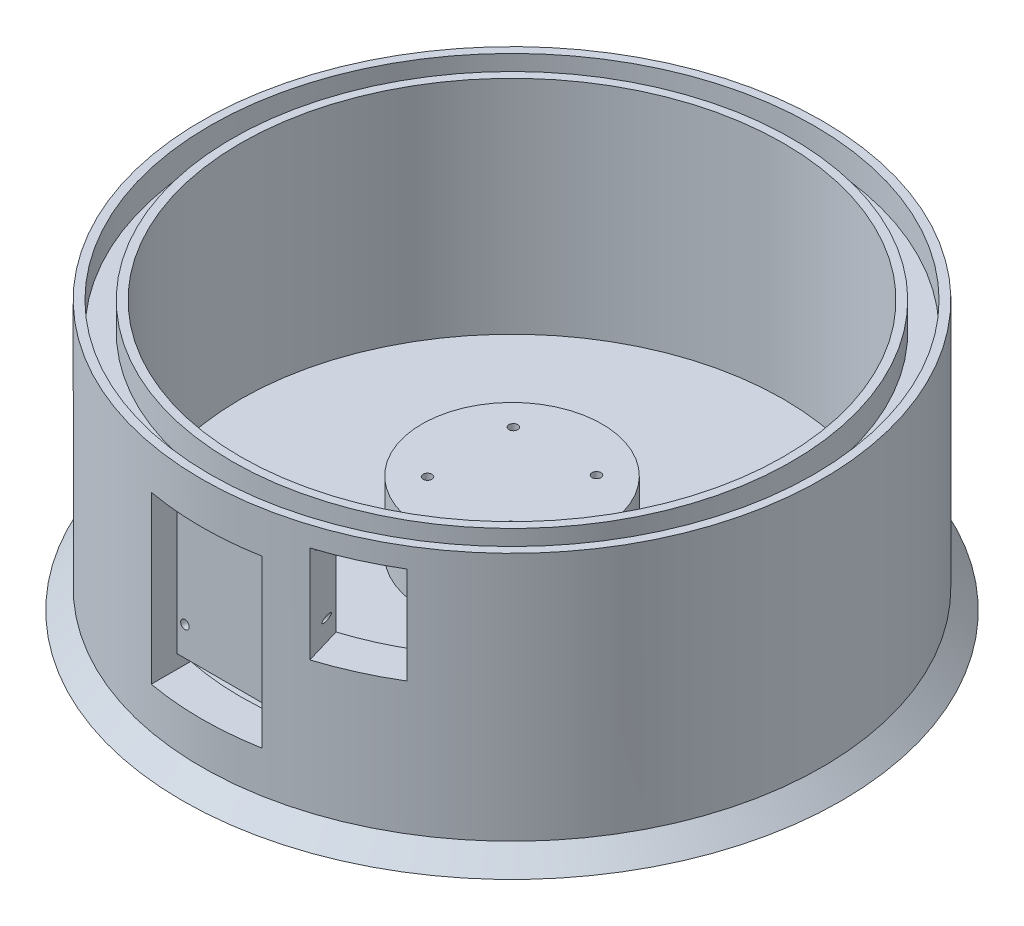
SolidWorks part; units mm, degrees
material "ABS"
ref_plane "Front Plane" through (0, 0, 0) normal (0, 0, 1) x (1, 0, 0)
ref_plane "Top Plane" through (0, 0, 0) normal (0, 1, 0) x (1, 0, 0)
ref_plane "Right Plane" through (0, 0, 0) normal (1, 0, 0) x (0, 0, -1)
sketch "Sketch1" plane through (0, 0, 0) normal (0, 1, 0) x (1, 0, 0)
  circle A1 centre (0, 0) radius 112
extrude "Boss-Extrude3" add sketch "Sketch1" along normal blind 90
ref_plane "Plane1" through (0, 0, 105) normal (0, 0, 1) x (1, 0, 0)
sketch "Sketch9" plane through (0, 90, 0) normal (0, 1, 0) x (1, 0, 0)
  circle A5 centre (0, 0) radius 101
  circle A7 centre (0, 0) radius 109
extrude "Cut-Extrude6" cut sketch "Sketch9" against normal blind 10
sketch "Sketch4" plane through (0, 0, 105) normal (0, 0, 1) x (1, 0, 0)
  line L26 (-20, 75) -> (20, 75)
  line L27 (-20, 75) -> (-20, 15)
  line L28 (-20, 15) -> (20, 15)
  line L29 (20, 75) -> (20, 15)
  line L30 (-20, 75) -> (20, 15) construction
  line L31 (-20, 15) -> (20, 75) construction
  point P5 (0, 45)
  dimension "D1" = 60
  dimension "D2" = 40
  dimension "D3" = 45
extrude "Cut-Extrude2" cut sketch "Sketch4" along normal blind 26 and the other way blind 4
sketch "Sketch12" plane through (0, 0, 0) normal (0, -1, 0) x (1, 0, 0)
  circle A1 centre (0, 0) radius 112
  circle A2 centre (0, 0) radius 112
  dimension "D1" = 0
extrude "Boss-Extrude4" add sketch "Sketch12" along normal blind 7 draft 45 draft outward yes
sketch "Sketch13" plane through (0, 90, 0) normal (0, 1, 0) x (1, 0, 0)
  circle A0 centre (0, 0) radius 98
extrude "Cut-Extrude8" cut sketch "Sketch13" against normal blind 80 contours A0
sketch "Sketch14" plane through (0, 0, 101) normal (0, 0, 1) x (1, 0, 0)
  circle A0 centre (-31.25, 55.25) radius 0.75
  circle A1 centre (31.25, 55.25) radius 0.75
  circle A2 centre (31.25, 7.75) radius 0.75
  circle A3 centre (-31.25, 7.75) radius 0.75
extrude "Cut-Extrude9" cut sketch "Sketch14" against normal blind 15
sketch "Sketch18" plane through (0, 10, 0) normal (0, 1, 0) x (1, 0, 0)
  circle A0 centre (0, 0) radius 32.5
  dimension "D1" = 65
extrude "Boss-Extrude5" add sketch "Sketch18" along normal blind 25
sketch "Sketch16" plane through (0, -7, 0) normal (0, -1, 0) x (1, 0, 0)
  line L0 (0, 0) -> (-8.9936, 0) construction
  line L1 (0, 0) -> (0, 9.8047) construction
  circle A2 centre (-15, 15.5) radius 1.6
  circle A5 centre (15, 15.5) radius 1.6
  circle A6 centre (15, -15.5) radius 1.6
  circle A7 centre (-15, -15.5) radius 1.6
  dimension "D3" = 3.2
  dimension "D1" = 15.5
  dimension "D2" = 15
extrude "Cut-Extrude11" cut sketch "Sketch16" against normal through all
sketch "Sketch17" plane through (0, -7, 0) normal (0, -1, 0) x (1, 0, 0)
  circle A0 centre (-15, 15.5) radius 3
  circle A1 centre (15, 15.5) radius 3
  circle A2 centre (-15, -15.5) radius 3
  circle A3 centre (15, -15.5) radius 3
  dimension "D1" = 6
  dimension "D2" = 6
  dimension "D3" = 6
  dimension "D4" = 6
extrude "Cut-Extrude12" cut sketch "Sketch17" against normal blind 30
sketch "Sketch19" plane through (0, -7, 0) normal (0, -1, 0) x (1, 0, 0)
  circle A0 centre (0, 0) radius 30
  dimension "D1" = 60
extrude "Cut-Extrude13" cut sketch "Sketch19" against normal blind 25 contours A0
sketch "Sketch20" plane through (0, 0, 101) normal (0, 0, 1) x (1, 0, 0)
  line L0 (20, 75) -> (20, 15) construction
  line L1 (-20, 15) -> (20, 15)
  line L2 (-20, 15) -> (-20, 20)
  line L3 (-20, 20) -> (20, 20)
  line L4 (20, 15) -> (20, 20)
  dimension "D1" = 5
extrude "Cut-Extrude14" cut sketch "Sketch20" against normal blind 25
sketch "Sketch21" plane through (0, 0, 101) normal (0, 0, 1) x (1, 0, 0)
  line L0 (20, 75) -> (-20, 75) construction
  circle A0 centre (12.45, 67.8) radius 1.55
  circle A1 centre (-12.45, 67.8) radius 1.55
  circle A2 centre (-17.05, 30.54) radius 1.55
  circle A3 centre (17.05, 30.54) radius 1.55
  dimension "D3" = 3.1
  dimension "D4" = 3.1
  dimension "D9" = 3.1
  dimension "D10" = 3.1
  dimension "D1" = 12.45
  dimension "D2" = 24.9
  dimension "D5" = 7.2
  dimension "D6" = 7.2
  dimension "D7" = 17.05
  dimension "D8" = 17.05
  dimension "D11" = 37.26
  dimension "D12" = 37.26
extrude "Cut-Extrude15" cut sketch "Sketch21" against normal blind 25
ref_plane "Plane2" through (22.2041, 47.7941, -296.4042) normal (0, 1, 0) x (1, 0, 0)
sketch "Sketch22" plane through (22.2041, 47.7941, -296.4042) normal (0, 1, 0) x (1, 0, 0)
  line L0 (-8.1019, -337.261) -> (12.405, -405.7625)
  line L1 (-8.1019, -337.261) -> (-1.3889, -334.1953)
  line L2 (-1.3889, -334.1953) -> (37.058, -394.3842)
  line L3 (12.405, -405.7625) -> (37.058, -394.3842)
extrude "Cut-Extrude16" cut sketch "Sketch22" along normal blind 35
